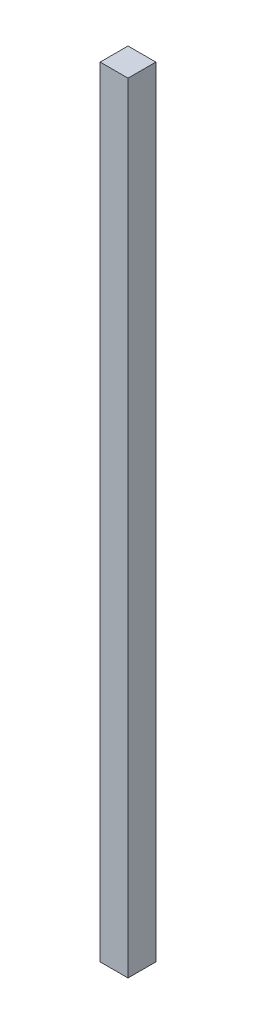
SolidWorks part; units mm, degrees
ref_plane "Front Plane" through (0, 0, 0) normal (0, 0, 1) x (1, 0, 0)
ref_plane "Top Plane" through (0, 0, 0) normal (0, 1, 0) x (1, 0, 0)
ref_plane "Right Plane" through (0, 0, 0) normal (1, 0, 0) x (0, 0, -1)
sketch "Sketch1" plane through (0, 0, 0) normal (0, 1, 0) x (1, 0, 0)
  line L1 (7.5, 7.5) -> (-7.5, 7.5)
  line L2 (7.5, 7.5) -> (7.5, -7.5)
  line L3 (7.5, -7.5) -> (-7.5, -7.5)
  line L4 (-7.5, 7.5) -> (-7.5, -7.5)
  line L5 (7.5, 7.5) -> (-7.5, -7.5) construction
  line L6 (7.5, -7.5) -> (-7.5, 7.5) construction
  point P0 (0, 0)
  dimension "D1" = 15
  dimension "D2" = 15
extrude "Boss-Extrude1" add sketch "Sketch1" along normal blind 420
